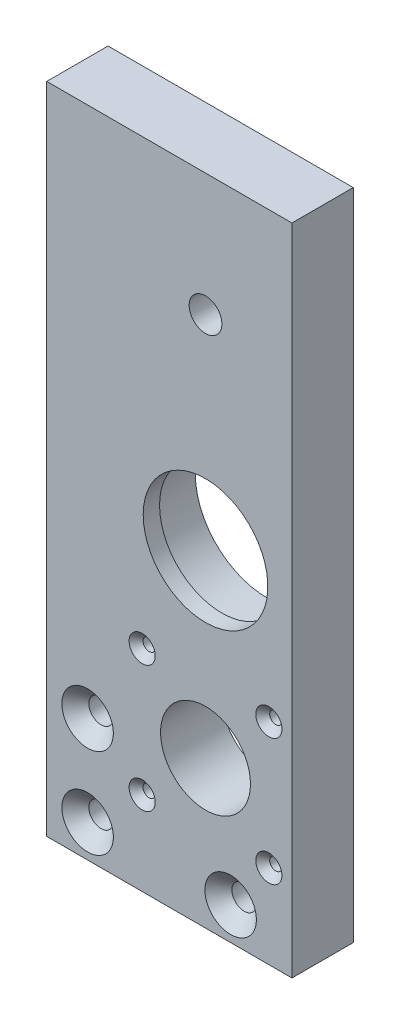
SolidWorks part; units mm, degrees
ref_plane "Ebene vorne" through (0, 0, 0) normal (0, 0, 1) x (1, 0, 0)
ref_plane "Ebene oben" through (0, 0, 0) normal (0, 1, 0) x (1, 0, 0)
ref_plane "Ebene rechts" through (0, 0, 0) normal (1, 0, 0) x (0, 0, -1)
sketch "Skizze1" plane through (0, 0, 0) normal (0, 0, 1) x (1, 0, 0)
  line L1 (0, 0) -> (65, 0)
  line L2 (0, 0) -> (0, 160)
  line L3 (0, 160) -> (65, 160)
  line L4 (65, 0) -> (65, 160)
  dimension "D1" = 160
  dimension "D2" = 65
extrude "Aufsatz-Linear austragen1" add sketch "Skizze1" along normal blind 15
sketch "Skizze2" plane through (0, 0, 0) normal (0, 0, -1) x (-1, 0, 0)
  line L0 (-65, 0) -> (-65, 160) construction
  line L2 (-65, 160) -> (0, 160) construction
  circle A0 centre (-43.85, 80) radius 17.5
  dimension "D1" = 35
  dimension "D2" = 80
  dimension "D3" = 21.15
extrude "Schnitt-Linear austragen1" cut sketch "Skizze2" against normal blind 11
sketch "Skizze4" plane through (0, 0, 11) normal (0, 0, -1) x (-1, 0, 0)
  line L0 (-65, 0) -> (-65, 160) construction
  line L1 (-65, 160) -> (0, 160) construction
  circle A0 centre (-43.85, 80) radius 15.25
  dimension "D2" = 30.5
  dimension "D1" = 21.15
  dimension "D3" = 80
extrude "Schnitt-Linear austragen3" cut sketch "Skizze4" against normal blind 10
sketch "Skizze5" plane through (0, 0, 15) normal (0, 0, 1) x (1, 0, 0)
  line L0 (0, 0) -> (65, 0) construction
  line L1 (65, 0) -> (65, 160) construction
  circle A0 centre (43.85, 36) radius 11
  dimension "D3" = 22
  dimension "D1" = 36
  dimension "D2" = 21.15
extrude "Schnitt-Linear austragen4" cut sketch "Skizze5" against normal blind 20
sketch "Skizze7" plane through (0, 0, 15) normal (0, 0, 1) x (1, 0, 0)
  line L0 (0, 160) -> (0, 0) construction
  line L1 (65, 0) -> (65, 160) construction
  line L2 (0, 0) -> (65, 0) construction
  circle A0 centre (15, 8) radius 3
  circle A1 centre (50, 8) radius 3
  dimension "D1" = 6
  dimension "D2" = 6
  dimension "D3" = 15
  dimension "D4" = 15
  dimension "D5" = 8
  dimension "D6" = 8
extrude "Schnitt-Linear austragen6" cut sketch "Skizze7" against normal blind 17
chamfer "Fase1" distance 3.3 angle 45 2 edges at (53, 8, 15) (18, 8, 15)
sketch "Skizze10" plane through (0, 0, 15) normal (0, 0, 1) x (1, 0, 0)
  line L0 (0, 0) -> (65, 0) construction
  line L1 (0, 160) -> (0, 0) construction
  circle A0 centre (15, 30) radius 3
  dimension "D1" = 6
  dimension "D2" = 30
  dimension "D3" = 15
extrude "Schnitt-Linear austragen9" cut sketch "Skizze10" against normal blind 29
chamfer "Fase2" distance 3.3 angle 45 1 edges at (18, 30, 15)
sketch "Skizze11" plane through (0, 0, 15) normal (0, 0, 1) x (1, 0, 0)
  line L0 (65, 0) -> (65, 160) construction
  line L1 (0, 0) -> (65, 0) construction
  circle A0 centre (59.35, 51.5) radius 1.5
  circle A1 centre (59.35, 20.5) radius 1.5
  circle A2 centre (28.35, 51.5) radius 1.5
  circle A3 centre (28.35, 20.5) radius 1.5
  dimension "D1" = 3
  dimension "D2" = 3
  dimension "D3" = 3
  dimension "D4" = 3
  dimension "D5" = 5.65
  dimension "D6" = 5.65
  dimension "D7" = 31
  dimension "D8" = 31
  dimension "D9" = 20.5
  dimension "D10" = 20.5
  dimension "D11" = 31
  dimension "D12" = 31
extrude "Schnitt-Linear austragen10" cut sketch "Skizze11" against normal blind 44
chamfer "Fase3" distance 1.7 angle 45 4 edges at (60.85, 51.5, 15) (29.85, 51.5, 15) (29.85, 20.5, 15) (60.85, 20.5, 15)
sketch "Skizze13" plane through (0, 0, 15) normal (0, 0, 1) x (1, 0, 0)
  line L0 (65, 0) -> (65, 160) construction
  line L1 (65, 160) -> (0, 160) construction
  circle A0 centre (43.85, 130) radius 4
  dimension "D1" = 8
  dimension "D2" = 21.15
  dimension "D3" = 30
extrude "Schnitt-Linear austragen12" cut sketch "Skizze13" against normal blind 35
sketch "Skizze14" plane through (0, 0, 0) normal (-1, 0, 0) x (0, 0, 1)
  line L1 (0, 160) -> (15, 160)
  line L2 (0, 160) -> (0, 0)
  line L3 (0, 0) -> (15, 0)
  line L4 (15, 160) -> (15, 0)
extrude "Schnitt-Linear austragen13" cut sketch "Skizze14" against normal blind 5
